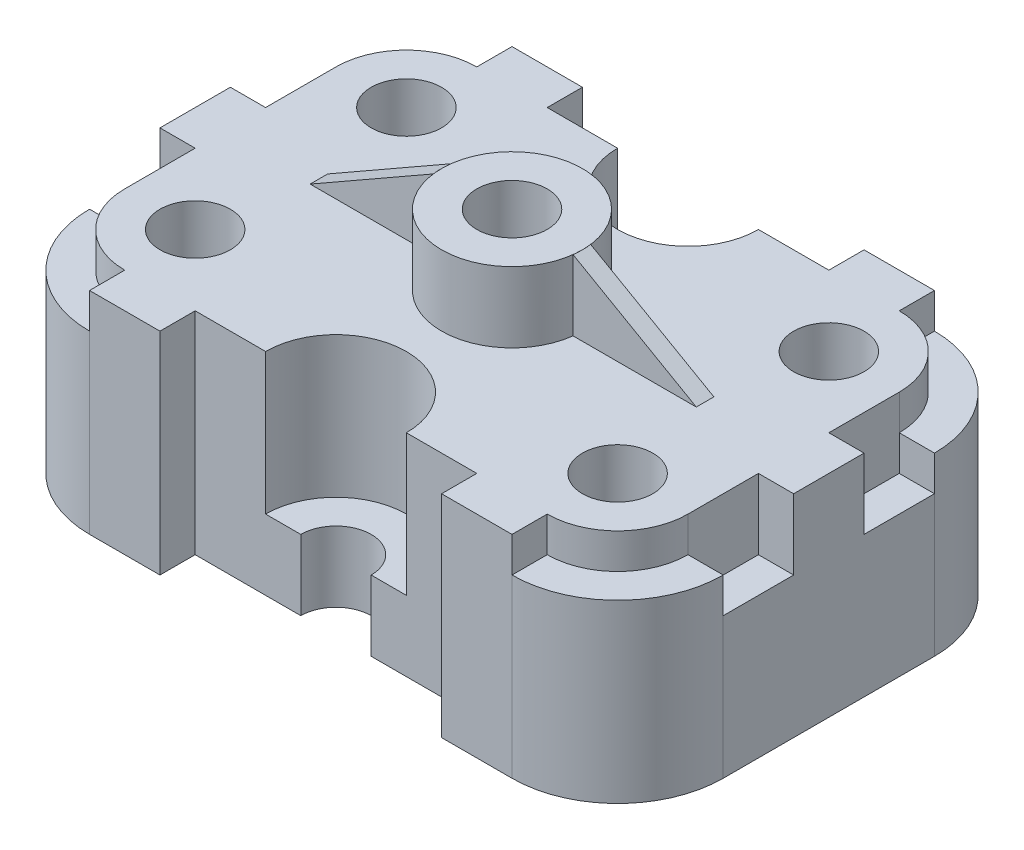
SolidWorks part; units mm, degrees
ref_plane "Front Plane" through (0, 0, 0) normal (0, 0, 1) x (1, 0, 0)
ref_plane "Top Plane" through (0, 0, 0) normal (0, 1, 0) x (1, 0, 0)
ref_plane "Right Plane" through (0, 0, 0) normal (1, 0, 0) x (0, 0, -1)
sketch "Sketch1" plane through (0, 0, 0) normal (0, 1, 0) x (1, 0, 0)
  line L1 (0, 0) -> (180, 0)
  line L2 (0, 0) -> (0, 120)
  line L3 (0, 120) -> (180, 120)
  line L4 (180, 0) -> (180, 120)
  dimension "D1" = 180
  dimension "D2" = 120
extrude "Boss-Extrude2" add sketch "Sketch1" along normal blind 80
sketch "Sketch2" plane through (0, 0, 0) normal (0, 1, 0) x (1, 0, 0)
  line L0 (180, 120) -> (0, 120) construction
  line L1 (50, 120) -> (130, 120)
  line L2 (50, 120) -> (50, 110)
  line L3 (50, 110) -> (130, 110)
  line L4 (130, 120) -> (130, 110)
  line L5 (0, 0) -> (180, 0) construction
  line L6 (50, 0) -> (130, 0)
  line L7 (50, 0) -> (50, 10)
  line L8 (50, 10) -> (130, 10)
  line L9 (130, 0) -> (130, 10)
  line L10 (0, 90) -> (0, 120)
  line L11 (0, 120) -> (30, 120)
  line L13 (180, 120) -> (0, 120)
  line L14 (180, 120) -> (180, 0)
  line L15 (180, 0) -> (0, 0)
  line L16 (0, 120) -> (0, 0)
  arc A0 (30, 120) -> (0, 90) centre (30, 90) ccw
  arc A1 (30, 0) -> (0, 30) centre (30, 30) cw
  arc A2 (150, 120) -> (180, 90) centre (150, 90) cw
  arc A3 (150, 0) -> (180, 30) centre (150, 30) ccw
  dimension "D8" = 30
  dimension "D13" = 30
  dimension "D17" = 30
  dimension "D20" = 30
  dimension "D25" = 30
  dimension "D1" = 10
  dimension "D2" = 10
  dimension "D3" = 50
  dimension "D4" = 50
  dimension "D5" = 50
  dimension "D6" = 50
  dimension "D7" = 30
  dimension "D9" = 30
  dimension "D10" = 90
  dimension "D11" = 150
  dimension "D12" = 30
  dimension "D14" = 30
  dimension "D15" = 30
  dimension "D16" = 90
  dimension "D18" = 30
  dimension "D19" = 30
  dimension "D21" = 30
  dimension "D22" = 180
  dimension "D23" = 50
  dimension "D24" = 30
  dimension "D26" = 30
extrude "Cut-Extrude1" cut sketch "Sketch2" along normal blind 150 contours L15 A1 L16 | A3 L15 L14 | L13 A2 L14 | L11 A0 L10
sketch "Sketch3" plane through (0, 0, 0) normal (0, 1, 0) x (1, 0, 0)
  line L0 (150, 120) -> (30, 120) construction
  line L1 (80, 120) -> (100, 120)
  line L2 (30, 0) -> (150, 0) construction
  line L3 (80, 0) -> (100, 0)
  arc A0 (100, 120) -> (80, 120) centre (90, 120) cw
  arc A1 (100, 0) -> (80, 0) centre (90, 0) ccw
  dimension "D1" = 20
  dimension "D2" = 50
  dimension "D3" = 20
  dimension "D4" = 50
extrude "Cut-Extrude2" cut sketch "Sketch3" along normal blind 150
sketch "Sketch4" plane through (0, 80, 0) normal (0, 1, 0) x (1, 0, 0)
  line L0 (80, 120) -> (30, 120) construction
  line L1 (30, 0) -> (80, 0) construction
  line L2 (150, 120) -> (100, 120) construction
  line L3 (180, 30) -> (180, 90) construction
  line L4 (100, 0) -> (150, 0) construction
  circle A0 centre (30, 90) radius 10
  circle A1 centre (150, 90) radius 10
  circle A2 centre (150, 30) radius 10
  circle A3 centre (30, 30) radius 10
  dimension "D1" = 20
  dimension "D2" = 20
  dimension "D3" = 20
  dimension "D4" = 20
  dimension "D5" = 30
  dimension "D6" = 30
  dimension "D7" = 30
  dimension "D8" = 30
  dimension "D9" = 30
  dimension "D10" = 30
  dimension "D11" = 30
  dimension "D12" = 30
extrude "Cut-Extrude3" cut sketch "Sketch4" against normal blind 150
sketch "Sketch5" plane through (0, 80, 0) normal (0, 1, 0) x (1, 0, 0)
  line L0 (80, 120) -> (30, 120) construction
  line L1 (150, 120) -> (100, 120) construction
  line L2 (70, 120) -> (80, 120)
  line L3 (100, 120) -> (110, 120)
  arc A0 (100, 120) -> (80, 120) centre (90, 120) cw
  arc A1 (110, 120) -> (70, 120) centre (90, 120) cw
  dimension "D1" = 10
extrude "Cut-Extrude4" cut sketch "Sketch5" against normal blind 60
sketch "Sketch6" plane through (0, 80, 0) normal (0, 1, 0) x (1, 0, 0)
  line L0 (30, 0) -> (80, 0) construction
  line L1 (100, 0) -> (150, 0) construction
  line L2 (70, 0) -> (110, 0)
  arc A0 (100, 0) -> (80, 0) centre (90, 0) ccw
  arc A1 (110, 0) -> (70, 0) centre (90, 0) ccw
  line M11 (30, 0) -> (80, 0)
  arc M12 (80, 0) -> (100, 0) centre (90, 0) cw
  line M13 (100, 0) -> (150, 0)
  dimension "D1" = 10
extrude "Cut-Extrude5" cut sketch "Sketch6" against normal blind 60 contours A1 M13 M11 M12
sketch "Sketch7" plane through (0, 80, 0) normal (0, 1, 0) x (1, 0, 0)
  circle A0 centre (90, 60) radius 10
  dimension "D1" = 20
  dimension "D2" = 60
  dimension "D3" = 90
extrude "Cut-Extrude7" cut sketch "Sketch7" against normal blind 139
sketch "Sketch8" plane through (0, 80, 0) normal (0, 1, 0) x (1, 0, 0)
  line L0 (70, 120) -> (30, 120) construction
  line L1 (50, 120) -> (130, 120)
  line L2 (50, 120) -> (50, 110)
  line L3 (50, 110) -> (130, 110)
  line L4 (130, 120) -> (130, 110)
  line L5 (30, 0) -> (70, 0) construction
  line L6 (50, 0) -> (130, 0)
  line L7 (50, 0) -> (50, 10)
  line L8 (50, 10) -> (130, 10)
  line L9 (130, 0) -> (130, 10)
  dimension "D1" = 10
  dimension "D2" = 50
  dimension "D3" = 50
  dimension "D4" = 50
  dimension "D5" = 10
  dimension "D6" = 50
extrude "Cut-Extrude8" cut sketch "Sketch8" against normal blind 139
sketch "Sketch9" plane through (0, 20, 0) normal (0, 1, 0) x (1, 0, 0)
  line L0 (107.3205, 110) -> (72.6795, 110) construction
  line L1 (72.6795, 110) -> (107.3205, 110)
  line L2 (107.3205, 10) -> (72.6795, 10) construction
  line L3 (72.6795, 10) -> (107.3205, 10)
  arc A0 (107.3205, 110) -> (72.6795, 110) centre (90, 120) cw
  arc A1 (107.3205, 10) -> (72.6795, 10) centre (90, 0) ccw
extrude "Boss-Extrude3" add sketch "Sketch9" along normal blind 60
sketch "Sketch10" plane through (0, 80, 0) normal (0, 1, 0) x (1, 0, 0)
  line L0 (50, 110) -> (130, 110) construction
  line L1 (130, 10) -> (50, 10) construction
  line L2 (80, 110) -> (100, 110)
  line L3 (80, 10) -> (100, 10)
  arc A0 (100, 110) -> (80, 110) centre (90, 110) cw
  arc A1 (100, 10) -> (80, 10) centre (90, 10) ccw
  dimension "D1" = 20
  dimension "D2" = 20
extrude "Cut-Extrude9" cut sketch "Sketch10" against normal blind 256
sketch "Sketch11" plane through (0, 80, 0) normal (0, 1, 0) x (1, 0, 0)
  line L1 (50, 110) -> (80, 110) construction
  line L2 (100, 110) -> (130, 110) construction
  line L3 (70, 110) -> (110, 110)
  arc A0 (100, 110) -> (80, 110) centre (90, 110) cw
  arc A1 (110, 110) -> (70, 110) centre (90, 110) cw
  line M16 (130, 110) -> (100, 110)
  arc M17 (100, 110) -> (80, 110) centre (90, 110) cw
  line M18 (80, 110) -> (50, 110)
  dimension "D1" = 10
extrude "Cut-Extrude10" cut sketch "Sketch11" against normal blind 60 contours A1 M16 M17 M18
sketch "Sketch12" plane through (0, 80, 0) normal (0, 1, 0) x (1, 0, 0)
  line L0 (80, 10) -> (50, 10) construction
  line L1 (130, 10) -> (100, 10) construction
  line L2 (70, 10) -> (110, 10)
  arc A0 (100, 10) -> (80, 10) centre (90, 10) ccw
  arc A1 (110, 10) -> (70, 10) centre (90, 10) ccw
  line M15 (50, 10) -> (80, 10)
  arc M16 (80, 10) -> (100, 10) centre (90, 10) cw
  line M17 (100, 10) -> (130, 10)
  dimension "D1" = 10
extrude "Cut-Extrude11" cut sketch "Sketch12" against normal blind 60 contours A1 M17 M15 M16
sketch "Sketch13" plane through (0, 0, 0) normal (1, 0, 0) x (0, 0, -1)
  line L1 (0, 80) -> (40, 80)
  line L2 (0, 80) -> (0, 60)
  line L3 (0, 60) -> (40, 60)
  line L4 (40, 80) -> (40, 60)
  line L5 (120, 80) -> (80, 80)
  line L6 (120, 80) -> (120, 60)
  line L7 (120, 60) -> (80, 60)
  line L8 (80, 80) -> (80, 60)
  line L9 (110, 60) -> (90, 60)
  line L10 (110, 60) -> (110, 50)
  line L11 (110, 50) -> (90, 50)
  line L12 (90, 60) -> (90, 50)
  line L13 (30, 60) -> (10, 60)
  line L14 (30, 60) -> (30, 50)
  line L15 (30, 50) -> (10, 50)
  line L16 (10, 60) -> (10, 50)
  dimension "D1" = 40
  dimension "D2" = 20
  dimension "D3" = 40
  dimension "D4" = 20
  dimension "D5" = 20
  dimension "D6" = 10
  dimension "D7" = 10
  dimension "D8" = 10
  dimension "D9" = 10
  dimension "D10" = 20
extrude "Cut-Extrude12" cut sketch "Sketch13" along normal blind 209 contours L5 L8 L7 L6 | L7 L12 L11 L10 | L4 L1 L2 L3 | L3 L16 L15 L14
sketch "Sketch14" plane through (0, 80, 0) normal (0, 1, 0) x (1, 0, 0)
  line L0 (0, 80) -> (180, 80)
  line L1 (180, 80) -> (180, 40)
  line L2 (180, 40) -> (0, 40)
  line L3 (0, 40) -> (0, 80)
  circle A0 centre (90, 60) radius 10
  circle A1 centre (90, 60) radius 20
  line M2 (0, 80) -> (0, 40)
  line M3 (0, 40) -> (180, 40)
  line M4 (180, 40) -> (180, 80)
  line M5 (180, 80) -> (0, 80)
  dimension "D1" = 20
  dimension "D2" = 40
  dimension "D3" = 180
  dimension "D4" = 180
extrude "Cut-Extrude13" cut sketch "Sketch14" against normal blind 20 contours A1 L0 M2 M3 | A1 L2 M4 M5
sketch "Sketch15" plane through (0, 60, 0) normal (0, 1, 0) x (1, 0, 0)
  line L0 (50, 110) -> (7.6393, 110) construction
  line L1 (7.6393, 110) -> (30, 110)
  line L2 (30, 110) -> (30, 120)
  arc A0 (30, 120) -> (7.6393, 110) centre (30, 90) ccw
extrude "Cut-Extrude14" cut sketch "Sketch15" against normal blind 10
sketch "Sketch16" plane through (0, 60, 0) normal (0, 1, 0) x (1, 0, 0)
  line L0 (30, 0) -> (30, 10)
  line L1 (50, 10) -> (7.6393, 10) construction
  line L2 (30, 10) -> (7.6393, 10)
  arc A0 (30, 0) -> (7.6393, 10) centre (30, 30) cw
  line M3 (50, 10) -> (7.6393, 10)
  arc M4 (7.6393, 10) -> (30, 0) centre (30, 30) ccw
extrude "Cut-Extrude15" cut sketch "Sketch16" against normal blind 10 contours L0 M4 M3
sketch "Sketch17" plane through (0, 60, 0) normal (0, 1, 0) x (1, 0, 0)
  line L0 (150, 0) -> (150, 10)
  line L1 (172.3607, 10) -> (130, 10) construction
  line L2 (150, 10) -> (172.3607, 10)
  arc A0 (150, 0) -> (172.3607, 10) centre (150, 30) ccw
  arc M1 (150, 0) -> (172.3607, 10) centre (150, 30) ccw
  line M2 (172.3607, 10) -> (130, 10)
extrude "Cut-Extrude16" cut sketch "Sketch17" against normal blind 10 contours L0 M1 M2
sketch "Sketch18" plane through (0, 60, 0) normal (0, 1, 0) x (1, 0, 0)
  line L0 (150, 120) -> (150, 110)
  line L1 (172.3607, 110) -> (130, 110) construction
  line L2 (150, 110) -> (172.3607, 110)
  arc A0 (150, 120) -> (172.3607, 110) centre (150, 90) cw
  arc M1 (172.3607, 110) -> (150, 120) centre (150, 90) ccw
  line M4 (130, 110) -> (172.3607, 110)
extrude "Cut-Extrude17" cut sketch "Sketch18" against normal blind 10 contours L0 M1 M4
sketch "Sketch19" plane through (0, 50, 0) normal (0, 1, 0) x (1, 0, 0)
  line L0 (180, 90) -> (160, 90) construction
  line L1 (150, 110) -> (110, 110)
  line L2 (70, 110) -> (50, 110) construction
  line L3 (70, 110) -> (30, 110)
  line L4 (20, 90) -> (0, 90) construction
  line L5 (10, 90) -> (20, 90)
  line L6 (90, 90) -> (40, 90) construction
  line L7 (40, 90) -> (140, 90)
  line L8 (160, 90) -> (170, 90)
  arc A0 (150, 110) -> (170, 90) centre (150, 90) cw
  arc A1 (110, 110) -> (70, 110) centre (90, 110) cw
  arc A2 (30, 110) -> (10, 90) centre (30, 90) ccw
  arc A3 (20, 90) -> (40, 90) centre (30, 90) cw
  arc A4 (140, 90) -> (160, 90) centre (150, 90) cw
  line M3 (150, 110) -> (130, 110)
  line M4 (130, 110) -> (110, 110)
  arc M5 (110, 110) -> (90, 90) centre (90, 110) cw
  line M6 (90, 90) -> (140, 90)
  arc M7 (140, 90) -> (160, 90) centre (150, 90) cw
  line M8 (160, 90) -> (180, 90)
extrude "Boss-Extrude4" add sketch "Sketch19" along normal blind 10 contours L5 A3 L7 A1 L3 A2 | A0 M3 M4 M5 M6 M7 M8
sketch "Sketch20" plane through (0, 50, 0) normal (0, 1, 0) x (1, 0, 0)
  line L0 (20, 30) -> (0, 30) construction
  line L1 (30, 0) -> (30, 10) construction
  line L2 (10, 30) -> (20, 30)
  line L3 (90, 30) -> (40, 30) construction
  line L4 (40, 30) -> (140, 30)
  line L5 (180, 30) -> (160, 30) construction
  line L6 (160, 30) -> (180, 30)
  line L7 (150, 10) -> (130, 10)
  line L8 (130, 10) -> (110, 10)
  line L9 (70, 10) -> (50, 10) construction
  line L10 (30, 10) -> (70, 10)
  arc A0 (10, 30) -> (30, 10) centre (30, 30) ccw
  arc A1 (20, 30) -> (40, 30) centre (30, 30) ccw
  arc A2 (140, 30) -> (160, 30) centre (150, 30) ccw construction
  arc A3 (140, 30) -> (160, 30) centre (150, 30) ccw
  arc A4 (170, 30) -> (150, 10) centre (150, 30) cw
  arc A5 (110, 10) -> (70, 10) centre (90, 10) ccw
  line M3 (30, 10) -> (50, 10)
  line M4 (50, 10) -> (70, 10)
  arc M5 (70, 10) -> (90, 30) centre (90, 10) cw
  line M6 (90, 30) -> (40, 30)
  arc M7 (40, 30) -> (20, 30) centre (30, 30) cw
  line M8 (20, 30) -> (0, 30)
extrude "Boss-Extrude5" add sketch "Sketch20" along normal blind 10 contours A0 M8 M3 M4 M5 M6 M7 | A5 L8 L7 A4 L6 A3 L4
sketch "Sketch21" plane through (0, 60, 0) normal (0, 1, 0) x (1, 0, 0)
  line L0 (0, 90) -> (0, 30) construction
  line L1 (0, 70) -> (10, 70)
  line L2 (0, 70) -> (0, 50)
  line L3 (0, 50) -> (10, 50)
  line L4 (10, 70) -> (10, 50)
  line L5 (180, 90) -> (180, 30) construction
  line L6 (180, 70) -> (170, 70)
  line L7 (180, 70) -> (180, 50)
  line L8 (180, 50) -> (170, 50)
  line L9 (170, 70) -> (170, 50)
  line L11 (10, 70) -> (0, 70)
  line L12 (10, 70) -> (10, 90)
  line L13 (10, 90) -> (0, 90)
  line L14 (0, 70) -> (0, 90)
  line L15 (10, 50) -> (0, 50)
  line L16 (10, 50) -> (10, 30)
  line L17 (10, 30) -> (0, 30)
  line L18 (0, 50) -> (0, 30)
  line L19 (170, 70) -> (180, 70)
  line L20 (170, 70) -> (170, 90)
  line L21 (170, 90) -> (180, 90)
  line L22 (180, 70) -> (180, 90)
  line L23 (170, 50) -> (180, 50)
  line L24 (170, 50) -> (170, 30)
  line L25 (170, 30) -> (180, 30)
  line L26 (180, 50) -> (180, 30)
  line M2 (170, 30) -> (180, 30)
  line M3 (180, 30) -> (180, 90)
  line M4 (180, 90) -> (170, 90)
  line M16 (10, 90) -> (0, 90)
  line M17 (0, 90) -> (0, 30)
  line M18 (0, 30) -> (10, 30)
  dimension "D1" = 10
  dimension "D2" = 20
  dimension "D3" = 20
  dimension "D4" = 10
  dimension "D5" = 20
  dimension "D6" = 20
extrude "Cut-Extrude20" cut sketch "Sketch21" against normal blind 20 contours L1 L12 M16 M17 | L16 L3 M17 M18 | L20 L6 M3 M4 | L8 L24 M2 M3
sketch "Sketch22" plane through (0, 60, 0) normal (0, 1, 0) x (1, 0, 0)
  line L0 (50, 10) -> (70, 10) construction
  line L1 (70, 110) -> (50, 110) construction
  line L2 (70.1569, 62.5) -> (35.1569, 62.5)
  line L4 (70.1569, 57.5) -> (35.1569, 57.5)
  line L5 (109.8431, 62.5) -> (144.8431, 62.5)
  line L6 (109.8431, 62.5) -> (109.8431, 57.5)
  line L7 (109.8431, 57.5) -> (144.8431, 57.5)
  line L8 (144.8431, 62.5) -> (144.8431, 57.5)
  line L9 (130, 10) -> (110, 10) construction
  line L10 (35.1569, 62.5) -> (35.1569, 57.5)
  line L13 (130, 110) -> (110, 110) construction
  circle A0 centre (90, 60) radius 20 construction
  arc A1 (70.1569, 62.5) -> (70.1569, 57.5) centre (90, 60) ccw
  dimension "D1" = 5
  dimension "D2" = 5
  dimension "D3" = 47.5
  dimension "D4" = 47.5
  dimension "D5" = 35
  dimension "D6" = 35
  dimension "D7" = 35
  dimension "D8" = 47.5
extrude "Boss-Extrude9" add sketch "Sketch22" along normal blind 19.999
sketch "Sketch23" plane through (0, 0, -57.5) normal (0, 0, 1) x (1, 0, 0)
  line L0 (35.1569, 60) -> (70.1569, 79.999)
  line L1 (70.1569, 79.999) -> (35.1569, 79.999)
  line L2 (35.1569, 79.999) -> (35.1569, 60)
  line L3 (109.8431, 79.999) -> (144.8431, 60)
  line L4 (144.8431, 60) -> (144.8431, 79.999)
  line L5 (144.8431, 79.999) -> (109.8431, 79.999)
  line L6 (109.8431, 79.999) -> (144.8431, 79.999) construction
  line L7 (109.8431, 79.999) -> (109.8431, 60) construction
extrude "Cut-Extrude21" cut sketch "Sketch23" against normal blind 10
equation "\"A\"=20"
